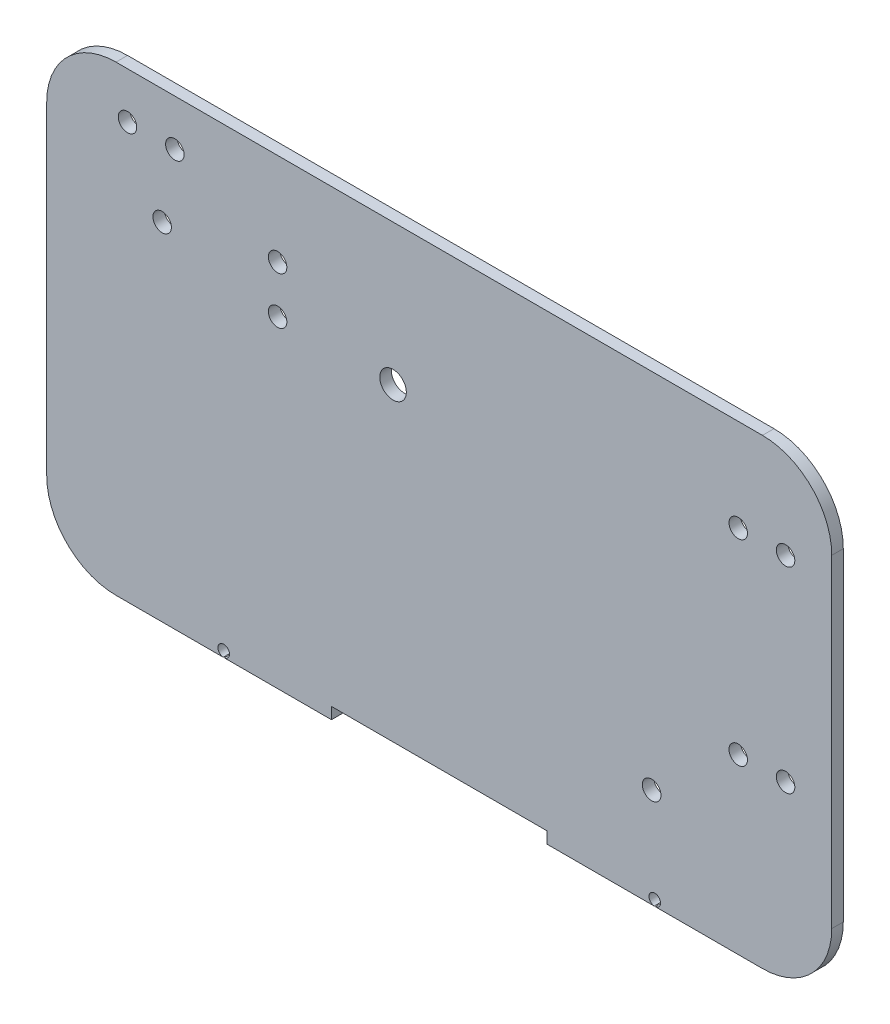
SolidWorks part; units mm, degrees
ref_plane "Alzado" through (0, 0, 0) normal (0, 0, 1) x (1, 0, 0)
ref_plane "Planta" through (0, 0, 0) normal (0, 1, 0) x (1, 0, 0)
ref_plane "Vista lateral" through (0, 0, 0) normal (1, 0, 0) x (0, 0, -1)
sketch "Croquis1" plane through (0, 0, 0) normal (0, 0, 1) x (1, 0, 0)
  line L0 (-125.4724, -88.3321) -> (154.5276, -88.3321)
  line L1 (184.5276, -58.3321) -> (184.5276, 81.6679)
  line L2 (154.5276, 111.6679) -> (-125.4724, 111.6679)
  line L3 (-155.4724, 81.6679) -> (-155.4724, -58.3321)
  arc A0 (-155.4724, -58.3321) -> (-125.4724, -88.3321) centre (-125.4724, -58.3321) ccw
  arc A1 (154.5276, -88.3321) -> (184.5276, -58.3321) centre (154.5276, -58.3321) ccw
  arc A2 (184.5276, 81.6679) -> (154.5276, 111.6679) centre (154.5276, 81.6679) ccw
  arc A3 (-125.4724, 111.6679) -> (-155.4724, 81.6679) centre (-125.4724, 81.6679) ccw
  circle A4 centre (-105.4724, 61.6679) radius 4
  circle A5 centre (-55.4724, 71.6679) radius 4
  circle A6 centre (-55.4724, 51.1679) radius 4
  circle A7 centre (144.0276, -13.3321) radius 4
  circle A8 centre (164.5276, -13.3321) radius 4
  circle A9 centre (144.0276, 71.6679) radius 4
  circle A10 centre (164.5276, 71.6679) radius 4
  circle A11 centre (-99.9724, 91.6679) radius 4
  circle A12 centre (-120.4724, 91.6679) radius 4
  circle A13 centre (-5.4724, 50.6679) radius 5.75
  circle A14 centre (106.5276, -45.3321) radius 4.05
  dimension "D1" = 8
  dimension "D2" = 30
  dimension "D18" = 11.5
  dimension "D21" = 8.1
  dimension "D22" = 157
  dimension "D3" = 144.0276
  dimension "D4" = 164.5276
  dimension "D5" = 184.5276
  dimension "D6" = 55.4724
  dimension "D7" = 99.9724
  dimension "D8" = 105.4724
  dimension "D9" = 120.4724
  dimension "D10" = 155.4724
  dimension "D11" = 51.1679
  dimension "D12" = 61.6679
  dimension "D13" = 71.6679
  dimension "D14" = 91.6679
  dimension "D15" = 111.6679
  dimension "D16" = 13.3321
  dimension "D17" = 88.3321
  dimension "D19" = 61
  dimension "D20" = 150
  dimension "D23" = 78
extrude "Saliente-Extruir1" add sketch "Croquis1" along normal blind 5
sketch "Croquis3" plane through (0, 0, 5) normal (0, 0, 1) x (1, 0, 0)
  line L0 (-32.1391, -83.3321) -> (-32.1391, -88.3321)
  line L1 (-125.4724, -88.3321) -> (154.5276, -88.3321)
  line L2 (-125.4724, -88.3321) -> (-125.4724, -83.3321)
  line L3 (-125.4724, -83.3321) -> (154.5276, -83.3321)
  line L4 (154.5276, -88.3321) -> (154.5276, -83.3321)
  line L5 (61.1942, -83.3321) -> (61.1942, -88.3321)
  line M10 (-125.4724, -88.3321) -> (154.5276, -88.3321)
  dimension "D1" = 5
  dimension "D2" = 93.3333
  dimension "D3" = 93.3333
extrude "Cortar-Extruir1" cut sketch "Croquis3" against normal blind 10 contours L5 L3 L0 M10
sketch "Croquis6" plane through (0, 0, 5) normal (0, 0, 1) x (1, 0, 0)
  line L0 (-78.8058, -88.3321) -> (-78.8058, -85.8421) construction
  line L1 (-125.4724, -88.3321) -> (-32.1391, -88.3321) construction
  line L2 (14.5276, -83.3321) -> (14.5276, -88.3321) construction
  line L3 (-32.1391, -83.3321) -> (61.1942, -83.3321) construction
  circle A0 centre (-78.8058, -85.8421) radius 2.5
  circle A1 centre (107.8609, -85.8421) radius 2.5
  dimension "D2" = 5
  dimension "D1" = 2.49
extrude "Cortar-Extruir2" cut sketch "Croquis6" against normal blind 10
sketch "Croquis7" plane through (0, 0, 5) normal (0, 0, 1) x (1, 0, 0)
  line L10 (108.0843, -88.3321) -> (154.5276, -88.3321)
  line L11 (184.5276, -58.3321) -> (184.5276, 81.6679)
  line L12 (154.5276, 111.6679) -> (-125.4724, 111.6679)
  line L13 (-155.4724, 81.6679) -> (-155.4724, -58.3321)
  line L14 (-125.4724, -88.3321) -> (-79.0291, -88.3321)
  line L15 (-78.5824, -88.3321) -> (-32.1391, -88.3321)
  line L16 (-32.1391, -88.3321) -> (-32.1391, -83.3321)
  line L17 (-32.1391, -83.3321) -> (61.1942, -83.3321)
  line L18 (61.1942, -83.3321) -> (61.1942, -88.3321)
  line L19 (61.1942, -88.3321) -> (107.6375, -88.3321)
  line L20 (108.0843, -88.3321) -> (154.5276, -88.3321)
  line L21 (184.5276, -58.3321) -> (184.5276, 81.6679)
  line L22 (154.5276, 111.6679) -> (-125.4724, 111.6679)
  line L23 (-155.4724, 81.6679) -> (-155.4724, -58.3321)
  line L24 (-125.4724, -88.3321) -> (-79.0291, -88.3321)
  line L25 (-78.5824, -88.3321) -> (-32.1391, -88.3321)
  line L26 (-32.1391, -88.3321) -> (-32.1391, -83.3321)
  line L27 (-32.1391, -83.3321) -> (61.1942, -83.3321)
  line L28 (61.1942, -83.3321) -> (61.1942, -88.3321)
  line L29 (61.1942, -88.3321) -> (107.6375, -88.3321)
  circle A0 centre (164.5276, 71.6679) radius 4 construction
  circle A1 centre (144.0276, 71.6679) radius 4 construction
  circle A2 centre (164.5276, -13.3321) radius 4 construction
  circle A3 centre (144.0276, -13.3321) radius 4 construction
  circle A4 centre (-55.4724, 51.1679) radius 4 construction
  circle A5 centre (-55.4724, 71.6679) radius 4 construction
  arc A6 (108.0843, -88.3321) -> (107.6375, -88.3321) centre (107.8609, -85.8421) ccw
  arc A7 (154.5276, -88.3321) -> (184.5276, -58.3321) centre (154.5276, -58.3321) ccw
  arc A8 (184.5276, 81.6679) -> (154.5276, 111.6679) centre (154.5276, 81.6679) ccw
  arc A9 (-125.4724, 111.6679) -> (-155.4724, 81.6679) centre (-125.4724, 81.6679) ccw
  arc A10 (-155.4724, -58.3321) -> (-125.4724, -88.3321) centre (-125.4724, -58.3321) ccw
  arc A11 (-78.5824, -88.3321) -> (-79.0291, -88.3321) centre (-78.8058, -85.8421) ccw
  arc A12 (108.0843, -88.3321) -> (107.6375, -88.3321) centre (107.8609, -85.8421) ccw
  arc A13 (154.5276, -88.3321) -> (184.5276, -58.3321) centre (154.5276, -58.3321) ccw
  arc A14 (184.5276, 81.6679) -> (154.5276, 111.6679) centre (154.5276, 81.6679) ccw
  arc A15 (-125.4724, 111.6679) -> (-155.4724, 81.6679) centre (-125.4724, 81.6679) ccw
  arc A16 (-155.4724, -58.3321) -> (-125.4724, -88.3321) centre (-125.4724, -58.3321) ccw
  arc A17 (-78.5824, -88.3321) -> (-79.0291, -88.3321) centre (-78.8058, -85.8421) ccw
  circle A18 centre (-105.4724, 61.6679) radius 4 construction
  circle A19 centre (-99.9724, 91.6679) radius 4 construction
  circle A20 centre (-120.4724, 91.6679) radius 4 construction
  circle A21 centre (164.5276, 71.6679) radius 4
  circle A22 centre (144.0276, 71.6679) radius 4
  circle A23 centre (164.5276, -13.3321) radius 4
  circle A24 centre (144.0276, -13.3321) radius 4
  circle A25 centre (-55.4724, 51.1679) radius 4
  circle A26 centre (-55.4724, 71.6679) radius 4
  circle A27 centre (-105.4724, 61.6679) radius 4
  circle A28 centre (-99.9724, 91.6679) radius 4
  circle A29 centre (-120.4724, 91.6679) radius 4
  circle A30 centre (-5.4724, 50.6679) radius 5.75 construction
  circle A31 centre (-5.4724, 50.6679) radius 5.75
  circle A32 centre (106.5276, -45.3321) radius 4.05 construction
  circle A33 centre (106.5276, -45.3321) radius 4.05
  dimension "D1" = 0
